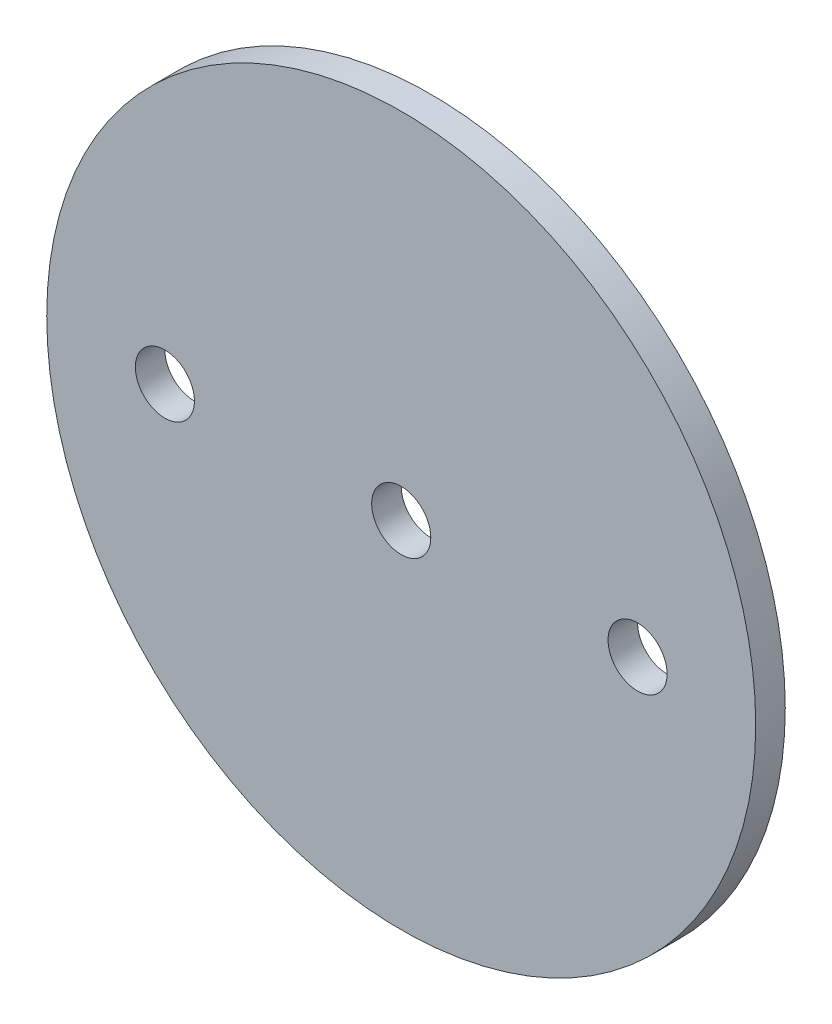
SolidWorks part; units mm, degrees
ref_plane "Front Plane" through (0, 0, 0) normal (0, 0, 1) x (1, 0, 0)
ref_plane "Top Plane" through (0, 0, 0) normal (0, 1, 0) x (1, 0, 0)
ref_plane "Right Plane" through (0, 0, 0) normal (1, 0, 0) x (0, 0, -1)
sketch "Sketch1" plane through (0, 0, 0) normal (0, 0, 1) x (1, 0, 0)
  circle A0 centre (0, 0) radius 38.1
  dimension "D1" = 76.2
extrude "Boss-Extrude1" add sketch "Sketch1" along normal mid plane 3.175
sketch "Sketch2" plane through (0, 0, 1.5875) normal (0, 0, 1) x (1, 0, 0)
  line L0 (-1000, 0) -> (49000, 0) construction
  point P1 (0, 0)
  point P4 (25.4, 0)
  point P5 (-25.4, 0)
  dimension "D1" = 25.4
  dimension "D2" = 50.8
hole_wizard "1/4 (0.25) Diameter Hole1" positions "Sketch2" profile "Sketch3" hole size "1/4" standard "ANSI Inch" end condition through all
sketch "Sketch3" plane through (-25.4, 0, 1.5875) normal (1, 0, 0) x (0, -1, 0)
  line L0 (0, 0) -> (0, 3.175)
  line L1 (0, 3.175) -> (3.175, 3.175)
  line L2 (3.175, 3.175) -> (3.175, 0)
  line L5 (3.175, 0) -> (0, 0)
  line L11 (0, -6.35) -> (0, 107.95) construction
  dimension "Thru Hole Dia." = 6.35
  dimension "Thru Hole Depth" = 3.175
equation "\"AIRFRAME_OD\"= 3.091in"
equation "\"AIRFRAME_ID\"= 3.00in"
equation "\"FLAT_T\"= 0.125in"
equation "\"NOSE_EXP_L\"= 3.5in"
equation "\"NOSE_SHOULDER_L\"= 5in"
equation "\"MAIN_L\"= 30in"
equation "\"RECO_COUP_L\"= 6in"
equation "\"RECO_SWITCH_L\"= 1.5in"
equation "\"DROGUE_L\"= 14in"
equation "\"ATS_FORE_COUP_L\"= 4in"
equation "\"ATS_AFT_COUP_L\"= 2.5in"
equation "\"LOWER_L\"= 16in"
equation "\"FIN_N\"= 4"
equation "\"CR_AFT_X\"= 0.5in"
equation "\"CR_FORE_X\"= 6in"
equation "\"FIN_ROOT\"= 5in"
equation "\"FIN_X\"= 0.75in"
equation "\"MOTOR_OD\"= 2.25in"
equation "\"MOTOR_ID\"= 2.126in"
equation "\"COUPLER_OD\"= 2.998in"
equation "\"COUPLER_ID\"= 2.875in"
equation "\"D1@Sketch1\"=\"AIRFRAME_ID\""
equation "\"D1@Boss-Extrude1\"=\"FLAT_T\""
equation "\"RECO_ROD_X\"= 1.5in"
equation "\"ATS_ROD_X\"= 2in"
equation "\"D1@Sketch2\"=\"ATS_ROD_X\"*0.5"
equation "\"D2@Sketch2\"=\"ATS_ROD_X\""
